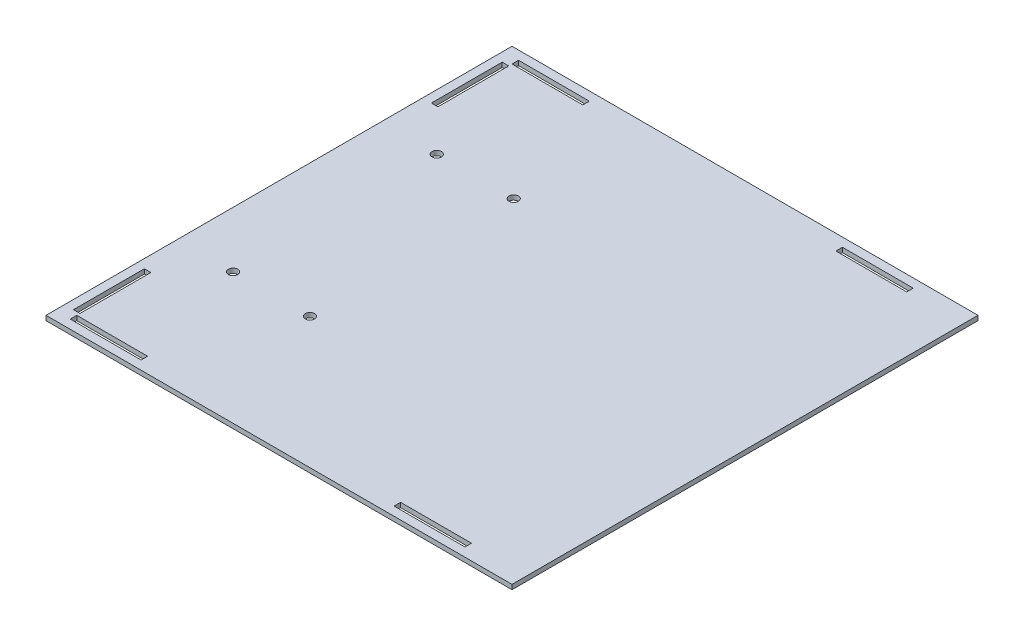
SolidWorks part; units mm, degrees
ref_plane "Front Plane" through (0, 0, 0) normal (0, 0, 1) x (1, 0, 0)
ref_plane "Top Plane" through (0, 0, 0) normal (0, 1, 0) x (1, 0, 0)
ref_plane "Right Plane" through (0, 0, 0) normal (1, 0, 0) x (0, 0, -1)
sketch "Sketch1" plane through (0, 0, 0) normal (0, 1, 0) x (1, 0, 0)
  line L1 (0, 63.5) -> (254, 63.5)
  line L2 (0, 63.5) -> (0, -63.5)
  line L3 (0, -63.5) -> (254, -63.5)
  line L4 (254, 63.5) -> (254, -63.5)
  line L5 (8.382, 58.674) -> (46.99, 58.674)
  line L6 (8.382, 58.674) -> (8.382, 55.118)
  line L7 (8.382, 55.118) -> (46.99, 55.118)
  line L8 (46.99, 58.674) -> (46.99, 55.118)
  line L9 (184.912, 58.674) -> (223.52, 58.674)
  line L10 (184.912, 58.674) -> (184.912, 55.118)
  line L11 (184.912, 55.118) -> (223.52, 55.118)
  line L12 (223.52, 58.674) -> (223.52, 55.118)
  line L13 (4.826, 53.34) -> (8.382, 53.34)
  line L14 (4.826, 53.34) -> (4.826, 14.732)
  line L15 (4.826, 14.732) -> (8.382, 14.732)
  line L16 (8.382, 53.34) -> (8.382, 14.732)
  dimension "D1" = 127
  dimension "D2" = 254
  dimension "D3" = 3.556
  dimension "D4" = 38.608
  dimension "D5" = 38.608
  dimension "D6" = 3.556
  dimension "D7" = 137.922
  dimension "D8" = 8.382
  dimension "D9" = 8.382
  dimension "D10" = 46.99
  dimension "D11" = 3.556
  dimension "D12" = 38.608
  dimension "D13" = 8.382
  dimension "D14" = 48.768
extrude "Boss-Extrude1" add sketch "Sketch1" along normal blind 2.54
hole_wizard "#7 (0.201) Diameter Hole1" positions "3DSketch1" profile "Sketch3" hole size "#7" standard "ANSI Inch" end condition through all
sketch3d "3DSketch1"
  line L0 (254, 2.54, -63.5) -> (0, 2.54, -63.5) construction
  line L1 (0, 2.54, -63.5) -> (0, 2.54, 63.5) construction
  point P0 (30.48, 2.54, 7.9756)
  point P2 (72.39, 2.54, 7.9756)
  dimension "D1" = 71.4756
  dimension "D2" = 30.48
  dimension "D3" = 41.91
sketch "Sketch3" plane through (30.48, 2.54, 7.9756) normal (1, 0, 0) x (0, 0, 1)
  line L0 (0, 0) -> (0, 2.54)
  line L1 (0, 2.54) -> (2.5527, 2.54)
  line L2 (2.5527, 2.54) -> (2.5527, 0)
  line L5 (2.5527, 0) -> (0, 0)
  line L11 (0, -6.35) -> (0, 107.95) construction
  dimension "Thru Hole Dia." = 5.1054
  dimension "Thru Hole Depth" = 2.54
mirror "Mirror1" about plane through (0, 2.54, 63.5) normal (0, 0, -1) of "Boss-Extrude1", "#7 (0.201) Diameter Hole1"
